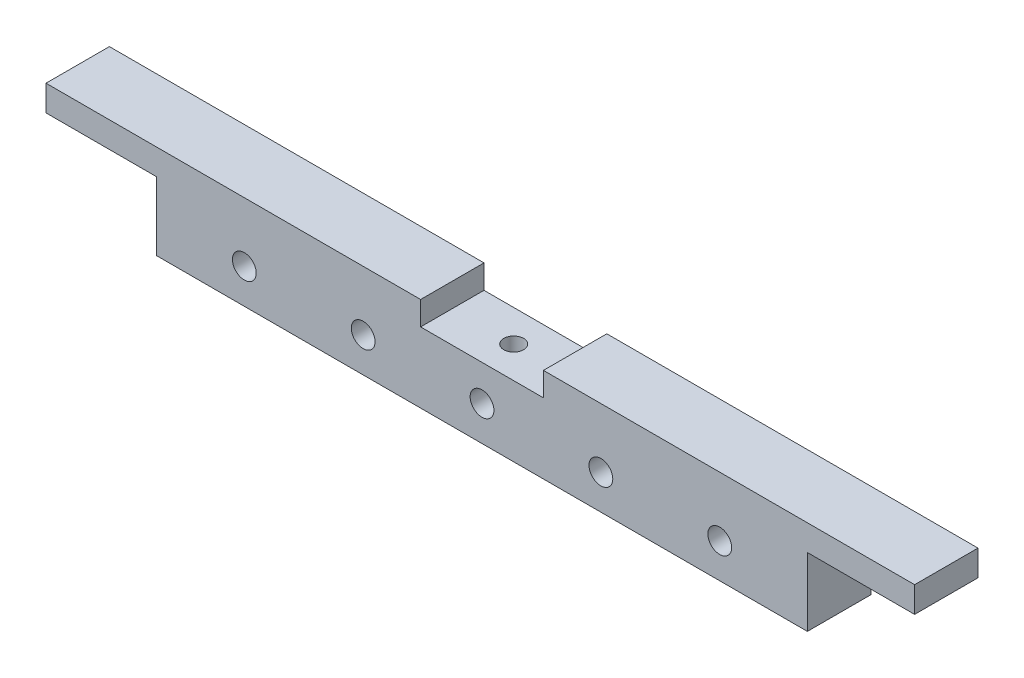
SolidWorks part; units mm, degrees
ref_plane "Alzado" through (0, 0, 0) normal (0, 0, 1) x (1, 0, 0)
ref_plane "Planta" through (0, 0, 0) normal (0, 1, 0) x (1, 0, 0)
ref_plane "Vista lateral" through (0, 0, 0) normal (1, 0, 0) x (0, 0, -1)
sketch "Croquis1" plane through (0, 0, 0) normal (0, 0, 1) x (1, 0, 0)
  line L0 (-197.6536, 0) -> (-8.5348, 0)
  line L1 (-8.5348, 0) -> (-8.5348, -12)
  line L2 (-8.5348, -12) -> (53.4652, -12)
  line L3 (53.4652, -12) -> (53.4652, 0)
  line L4 (53.4652, 0) -> (240.8464, 0)
  line L5 (240.8464, 0) -> (240.8464, -13)
  line L6 (186.7152, -13) -> (240.8464, -13)
  line L7 (186.7152, -13) -> (186.7152, -47.5)
  line L8 (186.7152, -47.5) -> (-141.7848, -47.5)
  line L9 (-141.7848, -47.5) -> (-141.7848, -13)
  line L10 (-141.7848, -13) -> (-197.6536, -13)
  line L11 (-197.6536, -13) -> (-197.6536, 0)
  line L12 (195.2485, -30) -> (-156.0149, -30) construction
  circle A0 centre (22.4652, -30) radius 6
  circle A1 centre (82.4652, -30) radius 6
  circle A2 centre (142.4652, -30) radius 6
  circle A3 centre (-37.5348, -30) radius 6
  circle A4 centre (-97.5348, -30) radius 6
  dimension "D9" = 12
  dimension "D10" = 12
  dimension "12" = 12
  dimension "D11" = 12
  dimension "D12" = 12
  dimension "D1" = 438.5
  dimension "D2" = 328.5
  dimension "D3" = 13
  dimension "D4" = 13
  dimension "D5" = 47.5
  dimension "D6" = 62
  dimension "D7" = 12
  dimension "D8" = 17.5
  dimension "D13" = 164.25
  dimension "D14" = 60
  dimension "D15" = 60
  dimension "D16" = 60
  dimension "D17" = 60
  dimension "D18" = 133.25
extrude "Saliente-Extruir1" add sketch "Croquis1" along normal blind 32
sketch "Croquis2" plane through (0, -12, 0) normal (0, 1, 0) x (1, 0, 0)
  line L0 (-8.5348, -16) -> (53.4652, -16) construction
  line L1 (-8.5348, -32) -> (-8.5348, 0) construction
  line L2 (53.4652, -32) -> (53.4652, 0) construction
  circle A0 centre (22.4652, -16) radius 5
  dimension "D1" = 10
extrude "Cortar-Extruir1" cut sketch "Croquis2" against normal blind 10
